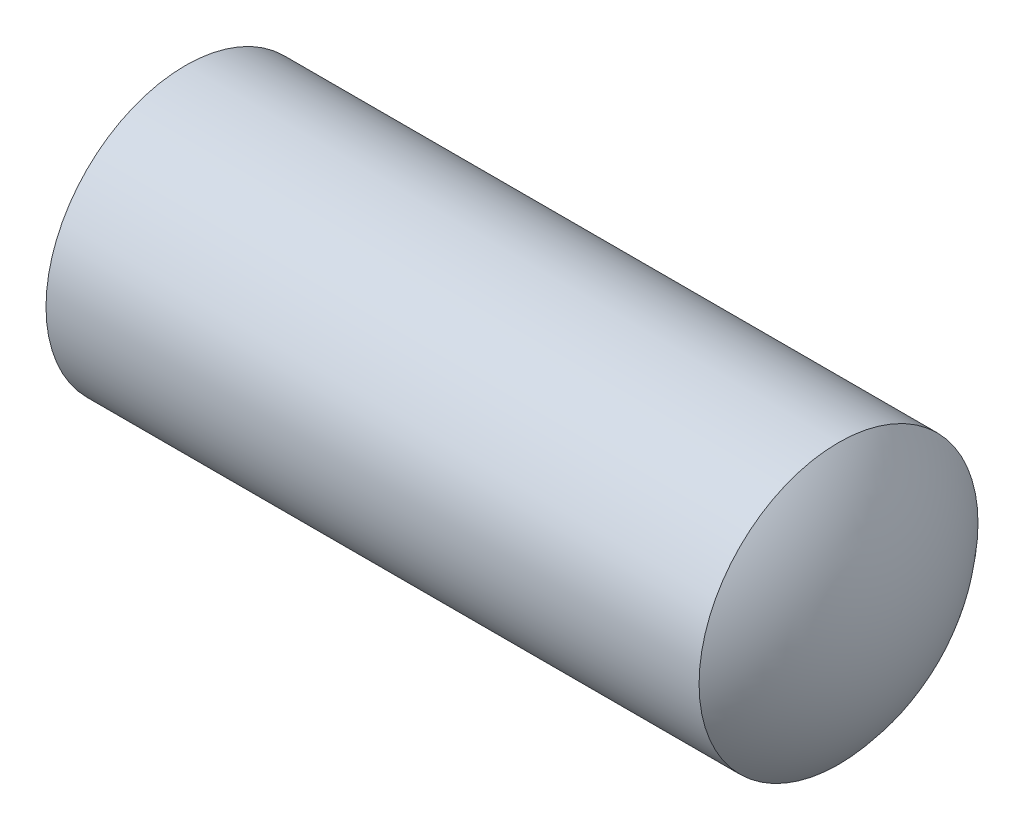
SolidWorks part; units mm, degrees
revolve "BaseBody" add sketch "BodySke" angle 360 about L5
sketch "BodySke" plane through (0, 0, 0) normal (0, 0, 1) x (1, 0, 0)
  line L0 (2.5522, -9.525) -> (47.1574, -9.525) construction
  line L1 (2.0066, 12.7) -> (2.0066, -9.525) construction
  line L2 (2.5522, 9.525) -> (47.1574, 9.525)
  line L4 (50.8, 0) -> (0, 0)
  line L5 (-12.7, 0) -> (88.9, 0) construction
  arc A0 (50.8, 0) -> (47.1574, 9.525) centre (36.5252, 0) ccw
  arc A1 (2.5522, 9.525) -> (0, 0) centre (19.05, 0) ccw
  dimension "Oval_radius" = 14.2748
  dimension "Crown_radius" = 19.05
  dimension "Length" = 50.8
  dimension "Diameter" = 19.05
  dimension "Advance" = 2.0066
cosmetic thread "ThreadCosmetic" [suppressed] parameters "Thread_minor"=16.0249
ref_plane "Plane1" through (0, 0, 0) normal (0, 0, 1) x (1, 0, 0)
ref_plane "Plane2" through (0, 0, 0) normal (0, 1, 0) x (1, 0, 0)
ref_plane "Plane3" through (0, 0, 0) normal (1, 0, 0) x (0, 0, -1)
sketch "ThdSchSke" plane through (0, 0, 0) normal (0, 0, 1) x (1, 0, 0)
  line L0 (2.5522, -8.0124) -> (1.4931, -9.525)
  line L1 (2.5522, -8.0124) -> (3.6113, -9.525)
  line L2 (3.6113, -9.525) -> (3.6113, -11.9063)
  line L3 (-3.175, 0) -> (5.1513, 0) construction
  line L4 (2.5522, -9.525) -> (2.5522, 9.525) construction
  line L5 (3.6113, -11.9063) -> (1.4931, -11.9063)
  line L6 (1.4931, -11.9063) -> (1.4931, -9.525)
  dimension "Thread_minor" = 16.0249
  dimension "Diameter" = 19.05
revolve "ThreadSchematic" [suppressed] cut sketch "ThdSchSke" angle 360 about L3
pattern_linear "ThdSchPat" [suppressed]
equation "\"Thread_minor@ThdSchSke\" = \"Thread_minor@ThreadCosmetic\""
equation "\"Diameter@ThdSchSke\" = \"Diameter@BodySke\""
equation "\"Overcut@ThdSchSke\" = \"Diameter@BodySke\" * 1.25"
equation "\"Num_threads@ThdSchPat\" = int ( ( \"Length@BodySke\" - ( \"Crown_radius@BodySke\" - sqr ( ( \"Crown_radius@BodySke\" * \"Crown_radius@BodySke\" ) - ( ( \"Diameter@BodySke\" * 0.5 ) * ( \"Diameter@BodySke\" * 0.5 ) ) ) ) - ( \"Oval_radius@BodySke\" - sqr ( ( \"Oval_radius@BodySke\" * \"Oval_radius@BodySke\" ) - ( ( \"Diameter@BodySke\" * 0.5 ) * ( \"Diameter@BodySke\" * 0.5 ) ) ) ) ) / \"Advance@BodySke\" + 0.999 )  + 1"
equation "\"Advance@ThdSchPat\" = ( \"Length@BodySke\" - ( \"Crown_radius@BodySke\" - sqr ( ( \"Crown_radius@BodySke\" * \"Crown_radius@BodySke\" ) - ( ( \"Diameter@BodySke\" * 0.5 ) * ( \"Diameter@BodySke\" * 0.5 ) ) ) ) - ( \"Oval_radius@BodySke\" - sqr ( ( \"Oval_radius@BodySke\" * \"Oval_radius@BodySke\" ) - ( ( \"Diameter@BodySke\" * 0.5 ) * ( \"Diameter@BodySke\" * 0.5 ) ) ) ) ) /  (\"Num_threads@ThdSchPat\" - 1) 'relax it"
equation "' \"Num_threads@ThdSchPat\" = \"Num_threads@ThdSchPat\" - sgn( \"Num_threads@ThdSchPat\" - 1) '---chamfered tips only---"
